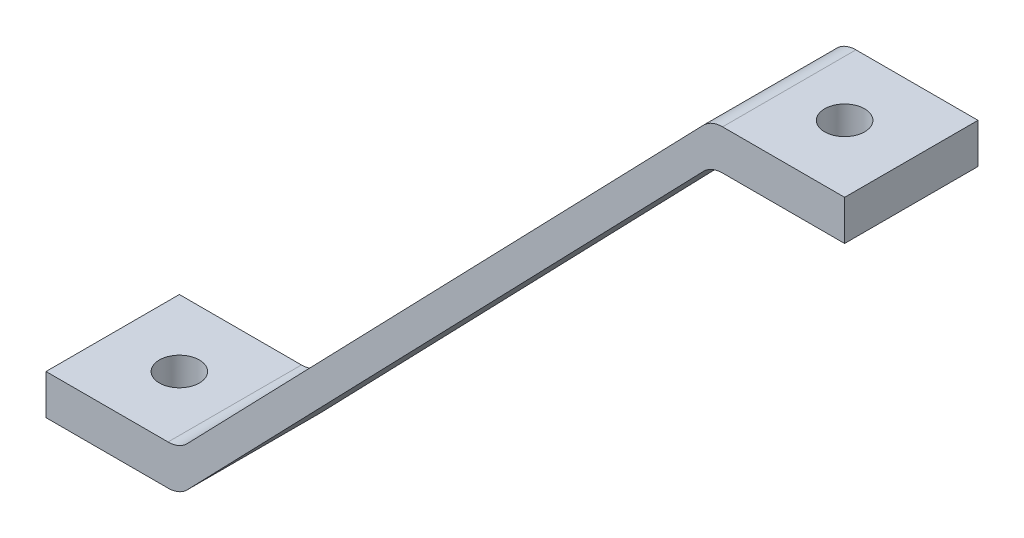
SolidWorks part; units mm, degrees
ref_plane "Front Plane" through (0, 0, 0) normal (0, 0, 1) x (1, 0, 0)
ref_plane "Top Plane" through (0, 0, 0) normal (0, 1, 0) x (1, 0, 0)
ref_plane "Right Plane" through (0, 0, 0) normal (1, 0, 0) x (0, 0, -1)
sketch "Sketch1" plane through (0, 0, 0) normal (0, 1, 0) x (1, 0, 0)
  line L1 (0, 0) -> (12.7, 0)
  line L2 (0, 0) -> (0, 12.7)
  line L3 (0, 12.7) -> (12.7, 12.7)
  line L4 (12.7, 0) -> (12.7, 12.7)
  dimension "D1" = 12.7
  dimension "D2" = 12.7
extrude "Boss-Extrude1" add sketch "Sketch1" along normal blind 3.81
sketch "Sketch2" plane through (0, 0, 0) normal (0, 0, 1) x (1, 0, 0)
  line L0 (12.7, 0) -> (63.3483, 52.3875)
  line L2 (63.3483, 56.1975) -> (12.7, 3.81)
  line L3 (12.7, 3.81) -> (12.7, 0)
  line L4 (319.8574, 56.1975) -> (40.4574, 56.1975) construction
  line L6 (63.3483, 52.3875) -> (76.0483, 52.3875)
  line L8 (63.3483, 56.1975) -> (76.0483, 56.1975)
  line L9 (76.0483, 52.3875) -> (76.0483, 56.1975)
  point P4 (81.8491, 56.1975)
  dimension "D1" = 12.7
  dimension "D2" = 3.81
extrude "Boss-Extrude2" add sketch "Sketch2" against normal up to surface (12.7 mm away) up to face at (6.35, 1.905, -12.7)
fillet "Fillet1" radius 2.54 4 edges at (63.3483, 56.1975, -6.35) (63.3483, 52.3875, -6.35) (12.7, 0, -6.35) (12.7, 3.81, -6.35)
sketch "Sketch6" plane through (0, 3.81, 0) normal (0, 1, 0) x (1, 0, 0)
  line L0 (0, 0) -> (11.6227, 0) construction
  line L1 (0, 12.7) -> (0, 0) construction
  line L2 (76.0483, 12.7) -> (76.0483, 0) construction
  line L3 (64.4256, 12.7) -> (76.0483, 12.7) construction
  circle A0 centre (6.35, 6.35) radius 1.905
  circle A1 centre (69.6983, 6.35) radius 1.905
  dimension "D1" = 3.81
  dimension "D2" = 6.35
  dimension "D3" = 6.35
  dimension "D4" = 6.35
  dimension "D5" = 6.35
extrude "Cut-Extrude1" cut sketch "Sketch6" against normal through all both and the other way through all contours A0 | A1
